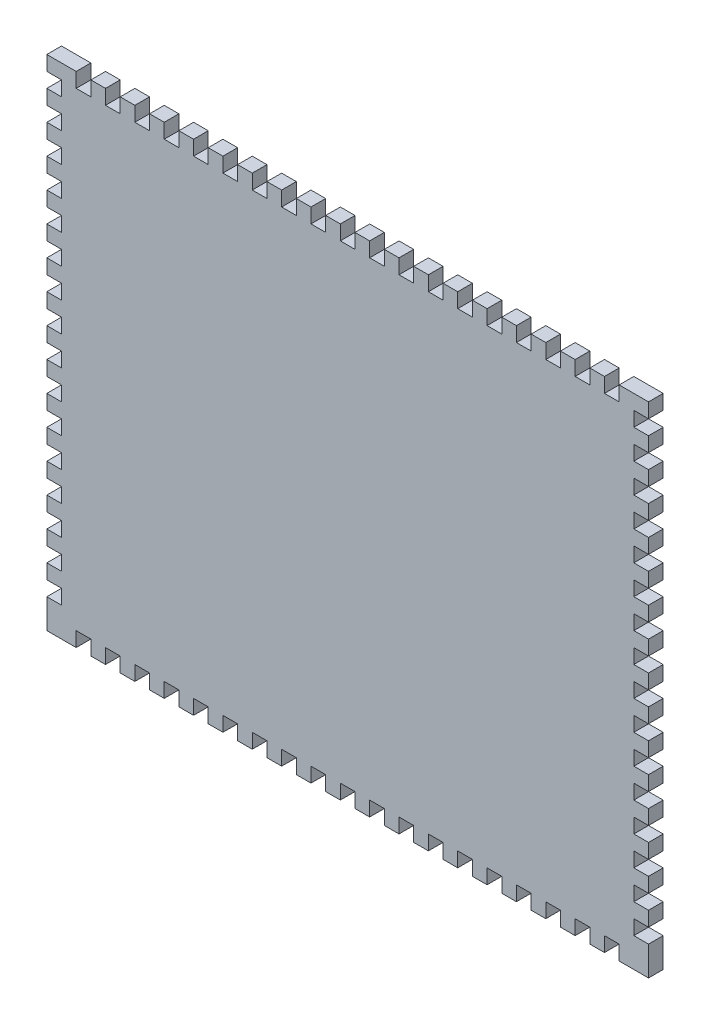
SolidWorks part; units mm, degrees
ref_plane "Front Plane" through (0, 0, 0) normal (0, 0, 1) x (1, 0, 0)
ref_plane "Top Plane" through (0, 0, 0) normal (0, 1, 0) x (1, 0, 0)
ref_plane "Right Plane" through (0, 0, 0) normal (1, 0, 0) x (0, 0, -1)
sketch "Sketch1" plane through (0, 0, 0) normal (0, 0, 1) x (1, 0, 0)
  line L1 (-130.175, -107.95) -> (130.175, -107.95)
  line L2 (-130.175, -107.95) -> (-130.175, 107.95)
  line L3 (-130.175, 107.95) -> (130.175, 107.95)
  line L4 (130.175, -107.95) -> (130.175, 107.95)
  line L5 (-130.175, -107.95) -> (130.175, 107.95) construction
  line L6 (-130.175, 107.95) -> (130.175, -107.95) construction
  point P0 (0, 0)
  dimension "D1" = 260.35
  dimension "D2" = 215.9
extrude "Boss-Extrude1" add sketch "Sketch1" along normal blind 6.35
sketch "Sketch2" plane through (0, 0, 6.35) normal (0, 0, 1) x (1, 0, 0)
  line L0 (-130.175, 107.95) -> (-130.175, -107.95) construction
  line L1 (-130.175, -88.9) -> (-123.825, -88.9)
  line L2 (-130.175, -88.9) -> (-130.175, -95.25)
  line L3 (-130.175, -95.25) -> (-123.825, -95.25)
  line L4 (-123.825, -88.9) -> (-123.825, -95.25)
  dimension "D1" = 12.7
  dimension "D2" = 6.35
  dimension "D3" = 6.35
extrude "Cut-Extrude1" cut sketch "Sketch2" against normal blind 6.35
pattern_linear "LPattern1" count 16 spacing 12.7 along (0, 1, 0) of "Cut-Extrude1"
mirror "Mirror1" about plane through (0, 0, 0) normal (1, 0, 0) of "LPattern1", "Cut-Extrude1"
sketch "Sketch3" plane through (0, 0, 6.35) normal (0, 0, 1) x (1, 0, 0)
  line L0 (130.175, 107.95) -> (-130.175, 107.95) construction
  line L1 (-117.475, 107.95) -> (-111.125, 107.95)
  line L2 (-117.475, 107.95) -> (-117.475, 101.6)
  line L3 (-117.475, 101.6) -> (-111.125, 101.6)
  line L4 (-111.125, 107.95) -> (-111.125, 101.6)
  dimension "D1" = 12.7
  dimension "D2" = 6.35
  dimension "D3" = 6.35
extrude "Cut-Extrude2" cut sketch "Sketch3" against normal through all and the other way through all
pattern_linear "LPattern2" count 19 spacing 12.7 along (1, 0, 0) of "Cut-Extrude2"
mirror "Mirror2" about plane through (0, 0, 0) normal (0, 1, 0) of "LPattern2", "Cut-Extrude2"
